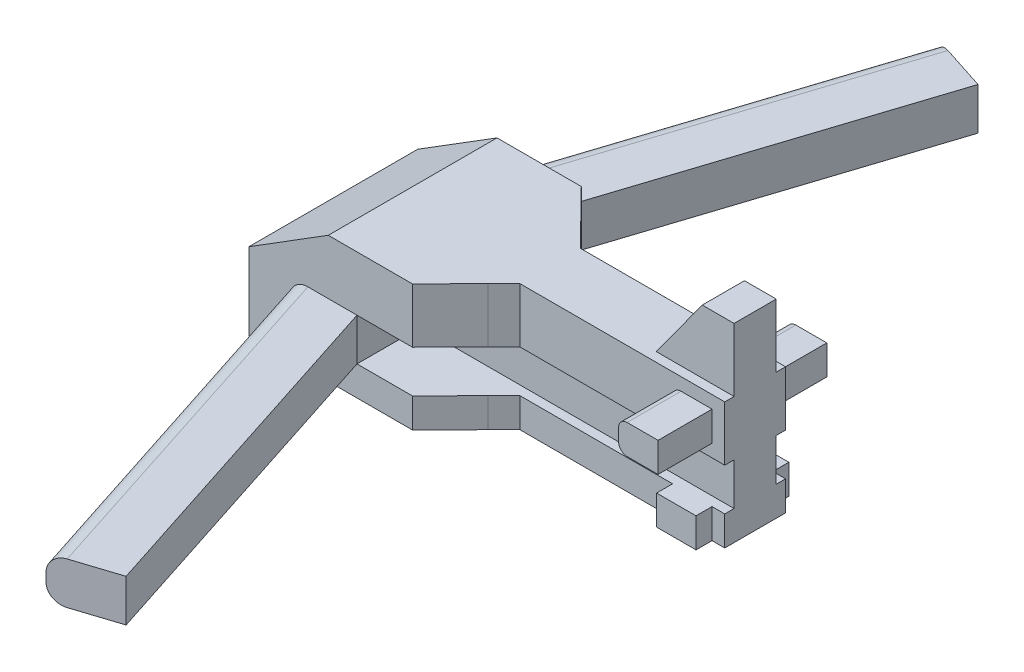
SolidWorks part; units mm, degrees
ref_plane "Front Plane" through (0, 0, 0) normal (0, 0, 1) x (1, 0, 0)
ref_plane "Top Plane" through (0, 0, 0) normal (0, 1, 0) x (1, 0, 0)
ref_plane "Right Plane" through (0, 0, 0) normal (1, 0, 0) x (0, 0, -1)
sketch "Sketch1" plane through (0, 0, 0) normal (0, 0, 1) x (1, 0, 0)
  line L0 (0, 0) -> (-69.85, 0)
  line L1 (-69.85, 0) -> (-69.85, 46.3734)
  line L2 (-69.85, 46.3734) -> (-22.0659, 76.2)
  line L3 (-22.0659, 76.2) -> (184.15, 76.2)
  line L4 (184.15, 76.2) -> (184.15, 0)
  line L5 (184.15, 0) -> (0, 0)
  point P3 (-69.85, 46.3734)
  point P8 (-22.0659, 76.2)
  dimension "D1" = 254
  dimension "D2" = 69.85
  dimension "D3" = 76.2
extrude "Boss-Extrude1" add sketch "Sketch1" against normal blind 101.6
sketch "Sketch3" plane through (0, 76.2, 0) normal (0, 1, 0) x (1, 0, 0)
  line L0 (-45.0193, 101.6) -> (25.443, 319.0696)
  line L1 (-22.0659, 101.6) -> (-69.85, 101.6) construction
  line L2 (25.443, 319.0696) -> (61.8645, 307.2686)
  line L3 (61.8645, 307.2686) -> (-4.7742, 101.6)
  line L4 (184.15, 101.6) -> (-22.0659, 101.6) construction
  line L5 (-4.7742, 101.6) -> (-45.0193, 101.6)
  line L6 (184.15, 50.8) -> (-334.58, 50.8) construction
  line L7 (184.15, 101.6) -> (184.15, 0) construction
  line L8 (-4.7742, 0) -> (-45.0193, 0)
  line L9 (61.8645, -205.6686) -> (-4.7742, 0)
  line L10 (25.443, -217.4696) -> (61.8645, -205.6686)
  line L11 (-45.0193, 0) -> (25.443, -217.4696)
  dimension "D1" = 36.4215
  dimension "D2" = 228.6
extrude "Boss-Extrude2" add sketch "Sketch3" against normal blind 25.4 from offset 33.02 offset against normal yes
sketch "Sketch4" plane through (0, 0, 0) normal (0, 0, 1) x (1, 0, 0)
  line L0 (-4.7742, 43.18) -> (-4.7742, 17.78)
  line L2 (-4.7742, 43.18) -> (190.2842, 43.18)
  line L3 (190.2842, 43.18) -> (190.2842, 17.78)
  line L4 (190.2842, 17.78) -> (-4.7742, 17.78)
extrude "Cut-Extrude1" cut sketch "Sketch4" against normal blind 38.1
sketch "Sketch5" plane through (0, 0, -101.6) normal (0, 0, -1) x (-1, 0, 0)
  line L0 (4.7742, 43.18) -> (4.7742, 17.78)
  line L3 (4.7742, 17.78) -> (-187.1243, 17.78)
  line L4 (-187.1243, 17.78) -> (-187.1243, 43.18)
  line L5 (-187.1243, 43.18) -> (4.7742, 43.18)
  point P6 (24.8968, 43.18)
extrude "Cut-Extrude4" cut sketch "Sketch5" against normal blind 38.1
sketch "Sketch6" plane through (0, 76.2, 0) normal (0, 1, 0) x (1, 0, 0)
  line L0 (28.6593, 0) -> (51.1284, 22.86)
  line L1 (184.15, 0) -> (-22.0659, 0) construction
  line L2 (51.1284, 22.86) -> (152.7525, 22.86)
  line L3 (152.7525, 22.86) -> (152.7525, 0)
  line L4 (152.7525, 0) -> (28.6593, 0)
  line L5 (-69.85, 50.8) -> (342.7194, 50.8) construction
  line L6 (-69.85, 101.6) -> (-69.85, 0) construction
  line L7 (152.7525, 78.74) -> (152.7525, 101.6)
  line L8 (51.1284, 78.74) -> (152.7525, 78.74)
  line L9 (28.6593, 101.6) -> (51.1284, 78.74)
  line L10 (152.7525, 101.6) -> (28.6593, 101.6)
  dimension "D1" = 22.86
extrude "Cut-Extrude5" cut sketch "Sketch6" against normal blind 101.6
sketch "Sketch8" plane through (0, 0, 0) normal (0, 0, 1) x (1, 0, 0)
  line L0 (184.15, 76.2) -> (184.15, 114.3156)
  line L1 (184.15, 114.3156) -> (165.0037, 114.3156)
  line L2 (165.0037, 114.3156) -> (137.3297, 76.2)
  line L3 (152.7525, 76.2) -> (51.1284, 76.2) construction
  line L4 (137.3297, 76.2) -> (184.15, 76.2)
extrude "Boss-Extrude3" add sketch "Sketch8" along normal blind 25.4 from offset 63.5 offset against normal yes
fillet "Fillet1" radius 10.16 1 edges at (-9.7881, 43.18, 108.7348)
fillet "Fillet2" radius 10.16 1 edges at (-9.7881, 17.78, 108.7348)
fillet "Fillet3" radius 10.16 1 edges at (-9.7881, 43.18, -210.3348)
fillet "Fillet4" radius 10.16 1 edges at (-9.7881, 17.78, -210.3348)
sketch "Sketch9" plane through (184.15, 0, 0) normal (1, 0, 0) x (0, 0, -1)
  line L0 (101.6, 17.78) -> (78.74, 17.78)
  line L1 (63.5, 17.78) -> (101.6, 17.78) construction
  line L2 (78.74, 17.78) -> (78.74, 0)
  line L3 (78.74, 0) -> (101.6, 0)
  line L4 (101.6, 0) -> (101.6, 17.78)
  line L5 (50.8, 114.3156) -> (50.8, -39.4696) construction
  line L6 (38.1, 114.3156) -> (63.5, 114.3156) construction
  line L7 (22.86, 0) -> (0, 0)
  line L8 (22.86, 17.78) -> (22.86, 0)
  line L9 (0, 17.78) -> (22.86, 17.78)
  line L10 (0, 0) -> (0, 17.78)
  dimension "D1" = 22.86
extrude "Cut-Extrude6" cut sketch "Sketch9" against normal blind 50.8
sketch "Sketch10" plane through (0, 76.2, 0) normal (0, 1, 0) x (1, 0, 0)
  line L0 (184.15, 32.4997) -> (176.494, 32.4997)
  line L1 (184.15, 38.1) -> (184.15, 0) construction
  line L2 (176.494, 32.4997) -> (176.494, 0)
  line L3 (184.15, 0) -> (152.7525, 0) construction
  line L4 (176.494, 0) -> (184.15, 0)
  line L5 (184.15, 0) -> (184.15, 32.4997)
  line L6 (184.15, 50.8) -> (1.1151, 50.8) construction
  line L7 (184.15, 38.1) -> (184.15, 63.5) construction
  line L8 (176.494, 101.6) -> (184.15, 101.6)
  line L9 (176.494, 69.1003) -> (176.494, 101.6)
  line L10 (184.15, 69.1003) -> (176.494, 69.1003)
  line L11 (184.15, 101.6) -> (184.15, 69.1003)
extrude "Cut-Extrude7" cut sketch "Sketch10" against normal through all
sketch "Sketch11" plane through (0, 76.2, 0) normal (0, 1, 0) x (1, 0, 0)
  line L0 (152.7525, 22.86) -> (152.7525, 32.4997)
  line L2 (51.1284, 22.86) -> (60.768, 32.4997)
  line L3 (60.768, 32.4997) -> (152.7525, 32.4997)
  line L4 (51.1284, 22.86) -> (152.7525, 22.86)
  line L5 (184.15, 50.8) -> (-11.0801, 50.8) construction
  line L6 (184.15, 38.1) -> (184.15, 63.5) construction
  line L7 (152.7525, 78.74) -> (152.7525, 69.1003)
  line L8 (51.1284, 78.74) -> (152.7525, 78.74)
  line L9 (51.1284, 78.74) -> (60.768, 69.1003)
  line L10 (60.768, 69.1003) -> (152.7525, 69.1003)
extrude "Cut-Extrude8" cut sketch "Sketch11" against normal through all
sketch "Sketch12" plane through (176.494, 0, 0) normal (1, 0, 0) x (0, 0, -1)
  line L0 (101.6, 76.2) -> (101.6, 68.58)
  line L1 (101.6, 43.18) -> (101.6, 76.2) construction
  line L2 (101.6, 68.58) -> (69.1003, 68.58)
  line L3 (69.1003, 43.18) -> (69.1003, 76.2) construction
  line L4 (69.1003, 68.58) -> (69.1003, 76.2)
  line L5 (69.1003, 76.2) -> (101.6, 76.2)
  line L6 (101.6, 59.69) -> (0, 59.69) construction
  line L7 (69.1003, 50.8) -> (69.1003, 43.18)
  line L8 (101.6, 50.8) -> (69.1003, 50.8)
  line L9 (101.6, 43.18) -> (101.6, 50.8)
  line L10 (69.1003, 43.18) -> (101.6, 43.18)
  line L11 (0, 43.18) -> (0, 76.2) construction
  line L12 (50.8, 59.69) -> (50.8, 120.5517) construction
  line L13 (50.8, 120.5517) -> (50.8, 18.9389) construction
  line L14 (0, 50.8) -> (32.4997, 50.8)
  line L15 (0, 43.18) -> (0, 50.8)
  line L16 (32.4997, 43.18) -> (0, 43.18)
  line L17 (32.4997, 50.8) -> (32.4997, 43.18)
  line L18 (32.4997, 68.58) -> (32.4997, 76.2)
  line L19 (0, 68.58) -> (32.4997, 68.58)
  line L20 (0, 76.2) -> (0, 68.58)
  line L21 (32.4997, 76.2) -> (0, 76.2)
  dimension "D1" = 7.62
extrude "Cut-Extrude9" cut sketch "Sketch12" against normal blind 50.8
fillet "Fillet6" radius 5.08 4 edges at (152.7525, 50.8, -85.3502) (152.7525, 68.58, -85.3502) (152.7525, 50.8, -16.2498) (152.7525, 68.58, -16.2498)
